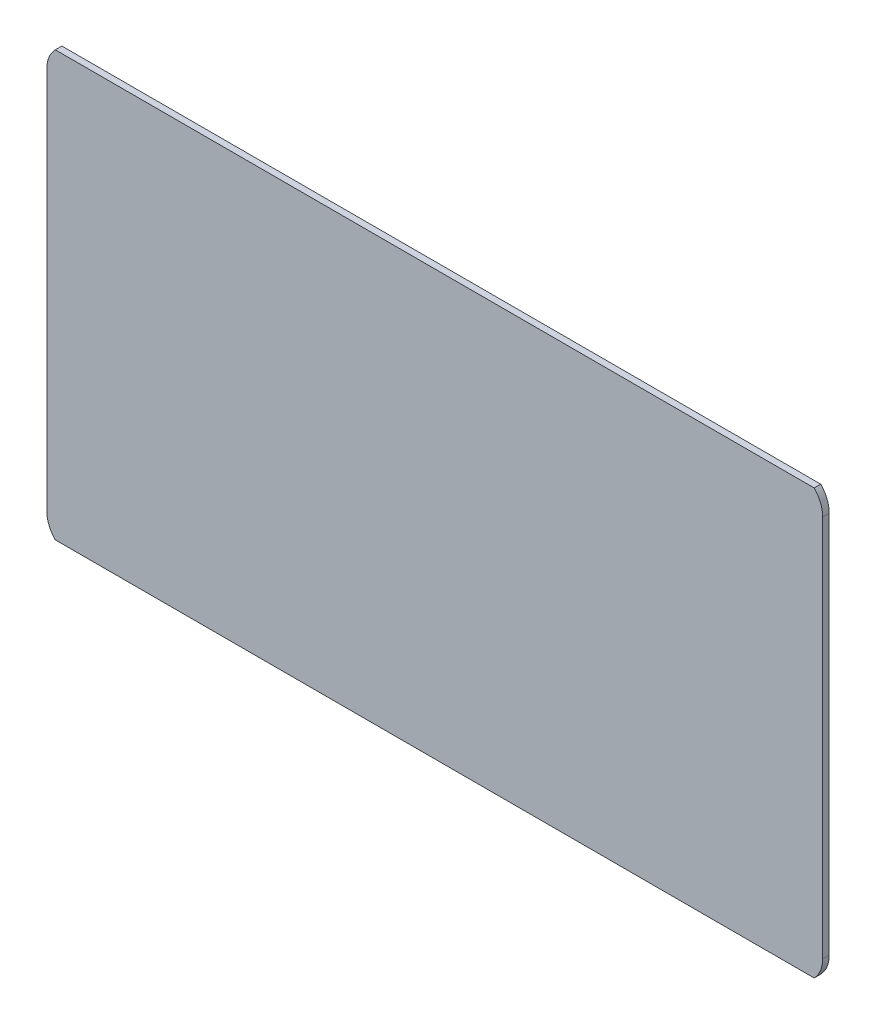
SolidWorks part; units mm, degrees
ref_plane "Alzado" through (0, 0, 0) normal (0, 0, 1) x (1, 0, 0)
ref_plane "Planta" through (0, 0, 0) normal (0, 1, 0) x (1, 0, 0)
ref_plane "Vista lateral" through (0, 0, 0) normal (1, 0, 0) x (0, 0, -1)
sketch "Croquis1" plane through (0, 0, 0) normal (0, 0, 1) x (1, 0, 0)
  line L1 (0, 0) -> (130.24, 0)
  line L2 (0, 0) -> (0, -71.24)
  line L3 (0, -71.24) -> (130.24, -71.24)
  line L4 (130.24, 0) -> (130.24, -71.24)
  dimension "D1" = 130.24
  dimension "D2" = 71.24
extrude "Base" add sketch "Croquis1" along normal blind 1.1
sketch "Croquis2" plane through (0, 0, 1.1) normal (0, 0, 1) x (1, 0, 0)
  line L0 (0, -71.24) -> (130.24, -71.24) construction
  line L1 (5, 1.5) -> (125.24, 1.5)
  line L2 (0, -3.5) -> (0, -67.74)
  line L3 (5, -72.74) -> (125.24, -72.74)
  line L4 (130.24, -3.5) -> (130.24, -67.74)
  line L6 (-6.2307, 7.2562) -> (133.5861, 7.2562)
  line L7 (-6.2307, 7.2562) -> (-6.2307, -75.6391)
  line L8 (-6.2307, -75.6391) -> (133.5861, -75.6391)
  line L9 (133.5861, 7.2562) -> (133.5861, -75.6391)
  arc A0 (125.24, -72.74) -> (130.24, -67.74) centre (125.24, -67.74) ccw
  arc A1 (125.24, 1.5) -> (130.24, -3.5) centre (125.24, -3.5) cw
  arc A2 (5, 1.5) -> (0, -3.5) centre (5, -3.5) ccw
  arc A3 (0, -67.74) -> (5, -72.74) centre (5, -67.74) ccw
  dimension "D3" = 5
  dimension "D1" = 74.24
  dimension "D2" = 1.5
extrude "Cortar-Extruir1" cut sketch "Croquis2" against normal blind 1.4
